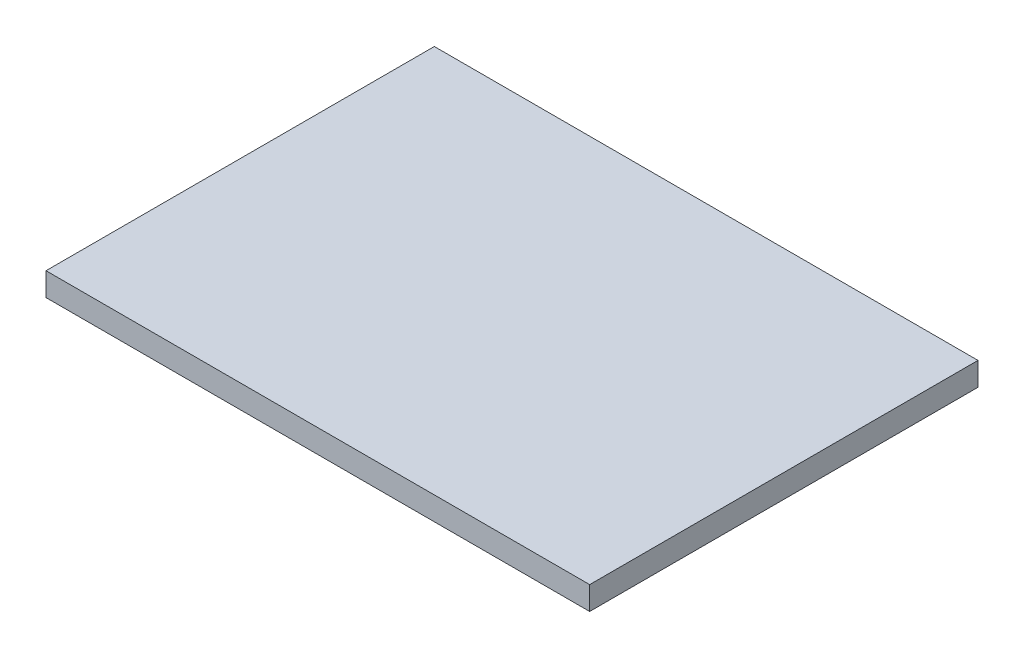
SolidWorks part; units mm, degrees
ref_plane "Alzado" through (0, 0, 0) normal (0, 0, 1) x (1, 0, 0)
ref_plane "Planta" through (0, 0, 0) normal (0, 1, 0) x (1, 0, 0)
ref_plane "Vista lateral" through (0, 0, 0) normal (1, 0, 0) x (0, 0, -1)
sketch "Croquis1" plane through (0, 0, 0) normal (0, 1, 0) x (1, 0, 0)
  line L1 (-35, 25) -> (35, 25)
  line L2 (-35, 25) -> (-35, -25)
  line L3 (-35, -25) -> (35, -25)
  line L4 (35, 25) -> (35, -25)
  line L5 (-35, 25) -> (35, -25) construction
  line L6 (-35, -25) -> (35, 25) construction
  point P0 (0, 0)
  dimension "D1" = 70
  dimension "D2" = 50
extrude "Saliente-Extruir1" add sketch "Croquis1" along normal blind 3
